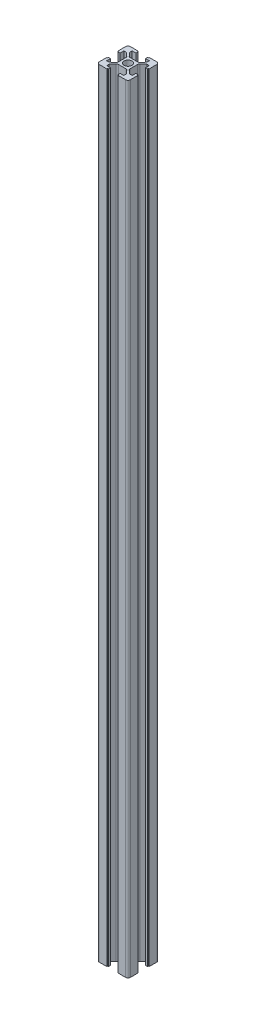
SolidWorks part; units mm, degrees
ref_plane "Front Plane" through (0, 0, 0) normal (0, 0, 1) x (1, 0, 0)
ref_plane "Top Plane" through (0, 0, 0) normal (0, 1, 0) x (1, 0, 0)
ref_plane "Right Plane" through (0, 0, 0) normal (1, 0, 0) x (0, 0, -1)
sketch "Sketch1" plane through (0, 0, 0) normal (0, 1, 0) x (1, 0, 0)
  line L0 (10, 0) -> (3.8, 0) construction
  line L1 (-8.5, -10) -> (8.5, -10)
  line L2 (-10, -8.5) -> (-10, 8.5)
  line L3 (-8.5, 10) -> (8.5, 10)
  line L4 (10, -8.5) -> (10, -3.6)
  line L5 (-10, -10) -> (10, 10) construction
  line L6 (-10, 10) -> (10, -10) construction
  line L7 (3.8, -2.4101) -> (3.8, 2.4101)
  line L8 (9.5, -3.1) -> (9.5, 3.1)
  line L9 (9.5, 3.1) -> (8.2, 3.1)
  line L10 (9.5, 3.1) -> (9.5, 3.6)
  line L11 (9.5, -3.1) -> (9.5, -3.6)
  line L12 (9.5, -3.6) -> (10, -3.6)
  line L13 (9.5, 3.6) -> (10, 3.6)
  line L14 (10, 3.6) -> (10, 8.5)
  line L15 (9.5, -3.1) -> (8.2, -3.1)
  line L16 (8.2, -3.1) -> (3.8, -3.1) construction
  line L17 (8.2, 3.1) -> (3.8, 3.1) construction
  line L18 (8.2, 3.1) -> (8.2, 5.5)
  line L19 (8.2, -3.1) -> (8.2, -5.5)
  line L20 (8.2, -5.5) -> (6.6, -5.5)
  line L21 (8.2, 5.5) -> (6.6, 5.5)
  line L22 (6.6, 5.5) -> (4.3238, 3.549)
  line L23 (6.6, -5.5) -> (4.3238, -3.549)
  line L24 (-5.5, -6.6) -> (-3.549, -4.3238)
  line L25 (-5.5, -8.2) -> (-5.5, -6.6)
  line L26 (-3.1, -8.2) -> (-5.5, -8.2)
  line L27 (-2.4101, -3.8) -> (2.4101, -3.8)
  line L28 (5.5, -6.6) -> (3.549, -4.3238)
  line L29 (5.5, -8.2) -> (5.5, -6.6)
  line L30 (3.1, -8.2) -> (5.5, -8.2)
  line L31 (3.1, -9.5) -> (3.1, -8.2)
  line L32 (3.1, -9.5) -> (3.6, -9.5)
  line L33 (3.6, -9.5) -> (3.6, -10)
  line L34 (-3.6, -9.5) -> (-3.6, -10)
  line L35 (-3.1, -9.5) -> (-3.6, -9.5)
  line L36 (-3.1, -9.5) -> (-3.1, -8.2)
  line L37 (-6.6, 5.5) -> (-4.3238, 3.549)
  line L38 (-8.2, 5.5) -> (-6.6, 5.5)
  line L39 (-8.2, 3.1) -> (-8.2, 5.5)
  line L40 (-3.8, 2.4101) -> (-3.8, -2.4101)
  line L41 (-6.6, -5.5) -> (-4.3238, -3.549)
  line L42 (-8.2, -5.5) -> (-6.6, -5.5)
  line L43 (-8.2, -3.1) -> (-8.2, -5.5)
  line L44 (-9.5, -3.1) -> (-8.2, -3.1)
  line L45 (-9.5, -3.1) -> (-9.5, -3.6)
  line L46 (-9.5, -3.6) -> (-10, -3.6)
  line L47 (-9.5, 3.6) -> (-10, 3.6)
  line L48 (-9.5, 3.1) -> (-9.5, 3.6)
  line L49 (-9.5, 3.1) -> (-8.2, 3.1)
  line L50 (5.5, 6.6) -> (3.549, 4.3238)
  line L51 (5.5, 8.2) -> (5.5, 6.6)
  line L52 (3.1, 8.2) -> (5.5, 8.2)
  line L53 (2.4101, 3.8) -> (-2.4101, 3.8)
  line L54 (-5.5, 6.6) -> (-3.549, 4.3238)
  line L55 (-5.5, 8.2) -> (-5.5, 6.6)
  line L56 (-3.1, 8.2) -> (-5.5, 8.2)
  line L57 (-3.1, 9.5) -> (-3.1, 8.2)
  line L58 (-3.1, 9.5) -> (-3.6, 9.5)
  line L59 (-3.6, 9.5) -> (-3.6, 10)
  line L60 (3.6, 9.5) -> (3.6, 10)
  line L61 (3.1, 9.5) -> (3.6, 9.5)
  line L62 (3.1, 9.5) -> (3.1, 8.2)
  circle A0 centre (0, 0) radius 2.5
  arc A1 (8.5, 10) -> (10, 8.5) centre (8.5, 8.5) cw
  arc A2 (8.5, -10) -> (10, -8.5) centre (8.5, -8.5) ccw
  arc A3 (-8.5, -10) -> (-10, -8.5) centre (-8.5, -8.5) cw
  arc A4 (-10, 8.5) -> (-8.5, 10) centre (-8.5, 8.5) cw
  arc A5 (3.8, -2.4101) -> (4.3238, -3.549) centre (5.3, -2.4101) ccw
  arc A6 (4.3238, 3.549) -> (3.8, 2.4101) centre (5.3, 2.4101) ccw
  arc A7 (-2.4101, -3.8) -> (-3.549, -4.3238) centre (-2.4101, -5.3) ccw
  arc A8 (3.549, -4.3238) -> (2.4101, -3.8) centre (2.4101, -5.3) ccw
  arc A9 (-3.8, 2.4101) -> (-4.3238, 3.549) centre (-5.3, 2.4101) ccw
  arc A10 (-4.3238, -3.549) -> (-3.8, -2.4101) centre (-5.3, -2.4101) ccw
  arc A11 (2.4101, 3.8) -> (3.549, 4.3238) centre (2.4101, 5.3) ccw
  arc A12 (-3.549, 4.3238) -> (-2.4101, 3.8) centre (-2.4101, 5.3) ccw
  point P0 (0, 0)
  point P25 (3.8, 0)
  point P28 (8.5, 0)
  dimension "D3" = 5
  dimension "D4" = 1.5
  dimension "D5" = 1.5
  dimension "D1" = 20
  dimension "D2" = 20
  dimension "D6" = 6.2
  dimension "D7" = 6.2
  dimension "D8" = 0.5
  dimension "D9" = 1.3
  dimension "D10" = 4
extrude "Boss-Extrude1" add sketch "Sketch1" along normal blind 500 contours A12 L54 L55 L56 L57 L58 L59 L3 A4 L2 L47 L48 L49 L39 L38 L37 A9 L40 A10 L41 L42 L43 L44 L45 L46 A3 L1 L34 L35 L36 L26 L25 L24 A7 L27 A8 L28 L29 L30 L31 L32 L33 A2 L4 L12 L11 L15 L19 L20
